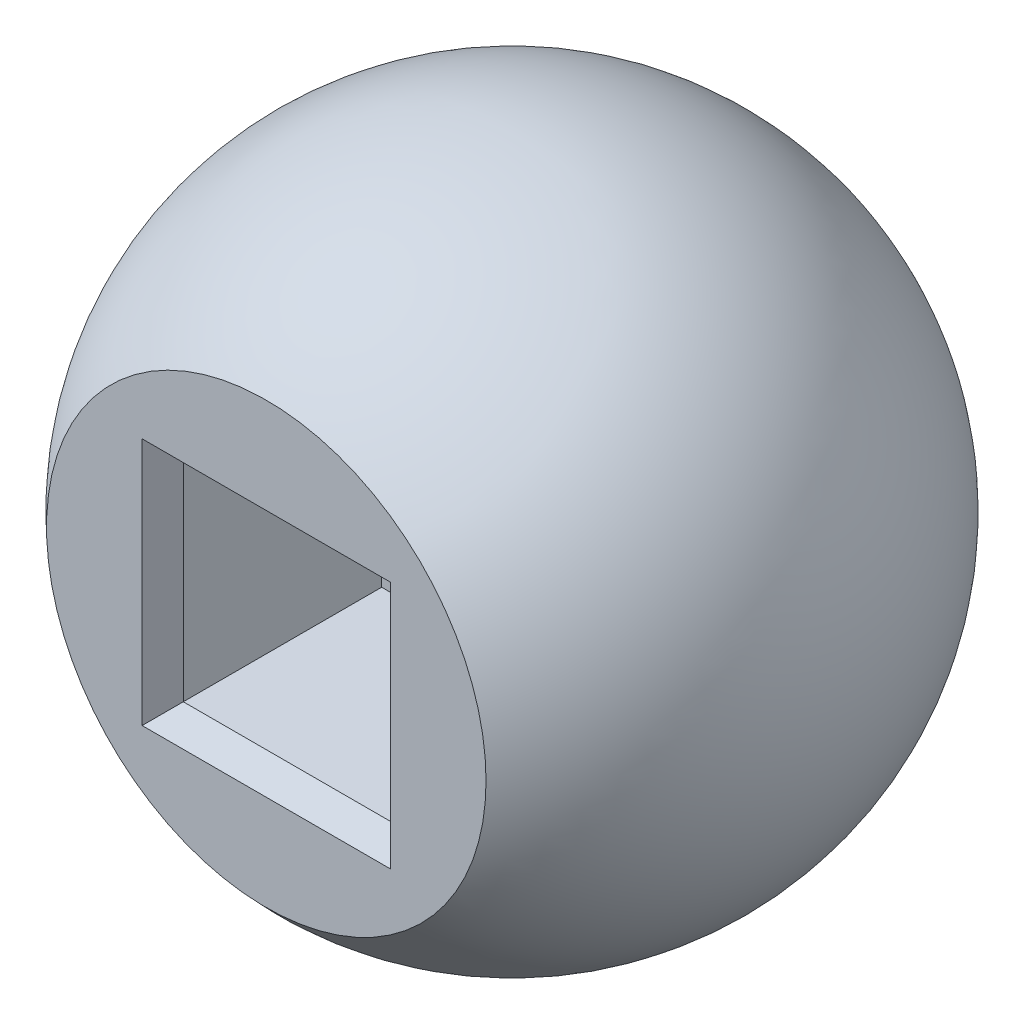
SolidWorks part; units mm, degrees
ref_plane "Спереди" through (0, 0, 0) normal (0, 0, 1) x (1, 0, 0)
ref_plane "Сверху" through (0, 0, 0) normal (0, 1, 0) x (1, 0, 0)
ref_plane "Справа" through (0, 0, 0) normal (1, 0, 0) x (0, 0, -1)
sketch "Sketch2" plane through (0, 0, 0) normal (0, 1, 0) x (1, 0, 0)
  line L0 (0, -15) -> (0, 15) construction
  line L1 (0, 15) -> (0, -11.1803)
  line L2 (0, -11.1803) -> (10, -11.1803)
  arc A0 (0, 15) -> (0, -15) centre (0, 0) cw construction
  arc A1 (0, 15) -> (10, -11.1803) centre (0, 0) cw
  point P4 (0, 0)
  dimension "D1" = 15
  dimension "D2" = 30
  dimension "D3" = 10
revolve "Revolve1" add sketch "Sketch2" angle 360 about L0
sketch "Sketch3" plane through (0, 0, 11.1803) normal (0, 0, 1) x (1, 0, 0)
  line L1 (-5.15, -5.15) -> (5.15, -5.15)
  line L2 (-5.15, -5.15) -> (-5.15, 5.15)
  line L3 (-5.15, 5.15) -> (5.15, 5.15)
  line L4 (5.15, -5.15) -> (5.15, 5.15)
  line L5 (-5.15, -5.15) -> (5.15, 5.15) construction
  line L6 (-5.15, 5.15) -> (5.15, -5.15) construction
  point P0 (0, 0)
  dimension "D1" = 10.3
  dimension "D2" = 10.3
extrude "Cut-Extrude1" cut sketch "Sketch3" against normal blind 10.4
sketch "Sketch4" plane through (0, 0, 0.7803) normal (0, 0, 1) x (1, 0, 0)
  circle A0 centre (0, 0) radius 2.15
  dimension "D1" = 4.3
extrude "Cut-Extrude2" cut sketch "Sketch4" against normal through all
sketch "Sketch5" plane through (0, 0, 0.7803) normal (0, 0, 1) x (1, 0, 0)
  circle A0 centre (0, 0) radius 4.5
  dimension "D1" = 9
extrude "Cut-Extrude3" cut sketch "Sketch5" against normal through all from offset 10 offset against normal yes
chamfer "Chamfer1" distance 0.5 angle 70 4 edges at (0, 5.15, 11.1803) (5.15, 0, 11.1803) (0, -5.15, 11.1803) (-5.15, 0, 11.1803)
